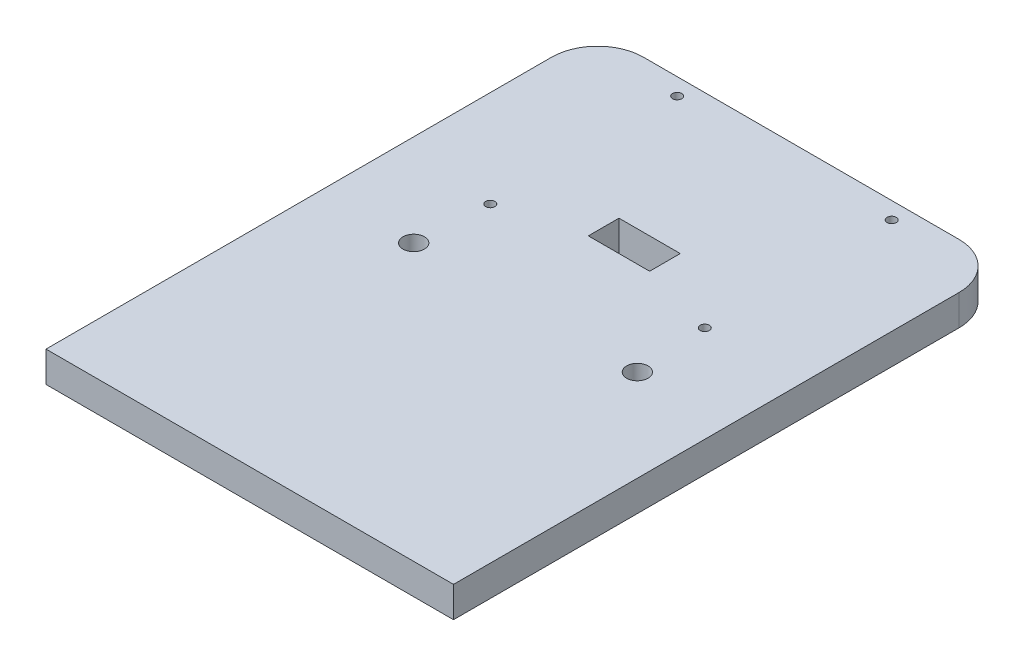
SolidWorks part; units mm, degrees
ref_plane "Front Plane" through (0, 0, 0) normal (0, 0, 1) x (1, 0, 0)
ref_plane "Top Plane" through (0, 0, 0) normal (0, 1, 0) x (1, 0, 0)
ref_plane "Right Plane" through (0, 0, 0) normal (1, 0, 0) x (0, 0, -1)
sketch "Sketch1" plane through (0, 0, 0) normal (0, 1, 0) x (1, 0, 0)
  line L0 (-66.5, -90) -> (66.5, 90)
  line L1 (-51.5, 90) -> (51.5, 90)
  line L2 (-66.5, 75) -> (-66.5, -90)
  line L3 (-66.5, -90) -> (66.5, -90)
  line L4 (66.5, 75) -> (66.5, -90)
  line L5 (-62.6432, 85.0413) -> (66.5, -90)
  line L6 (0, 141.8834) -> (0, -120.8453) construction
  line L7 (-104.8047, 0) -> (146.383, 0) construction
  line L8 (35, 83) -> (35, 23.5) construction
  line L9 (-35, 83) -> (-35, 23.5) construction
  line L10 (-33.5, 84.5) -> (33.5, 84.5) construction
  line L11 (33.5, 84.5) -> (33.5, 23.5) construction
  line L12 (33.5, 23.5) -> (-33.5, 23.5) construction
  line L13 (-10, 40.5) -> (10, 30.5) construction
  line L14 (-10, 40.5) -> (10, 40.5)
  line L15 (-10, 40.5) -> (-10, 30.5)
  line L16 (-10, 30.5) -> (10, 30.5)
  line L17 (10, 40.5) -> (10, 30.5)
  line L18 (-10, 30.5) -> (10, 40.5) construction
  arc A0 (66.5, 75) -> (51.5, 90) centre (51.5, 75) ccw
  arc A1 (-66.5, 75) -> (-51.5, 90) centre (-51.5, 75) cw
  circle A2 centre (36.5, 0) radius 3.5
  circle A3 centre (-35, 84.5) radius 1.5
  circle A4 centre (35, 84.5) radius 1.5
  circle A5 centre (35, 23.5) radius 1.5
  circle A6 centre (-35, 23.5) radius 1.5
  circle A7 centre (-36.5, 0) radius 3.5
  point P4 (0, 0)
  point P38 (0, 35.5)
  dimension "D3" = 15
  dimension "D4" = 15
  dimension "D1" = 7
  dimension "D5" = 30
  dimension "D6" = 3
  dimension "D7" = 5.5
  dimension "D9" = 35
  dimension "D12" = 3
  dimension "D2" = 180
  dimension "D8" = 31.5
  dimension "D10" = 133
  dimension "D11" = 59.5
  dimension "D13" = 20
  dimension "D14" = 10
  dimension "D15" = 7
extrude "Boss-Extrude1" add sketch "Sketch1" along normal blind 10 contours L5 L0 L3 | A1 L2 L0 L5 A6 A7 | L4 A0 L0 L5 A5 A2 | A1 L5 L0 A0 L1 L14 L17 L16 L15 A3 A4
